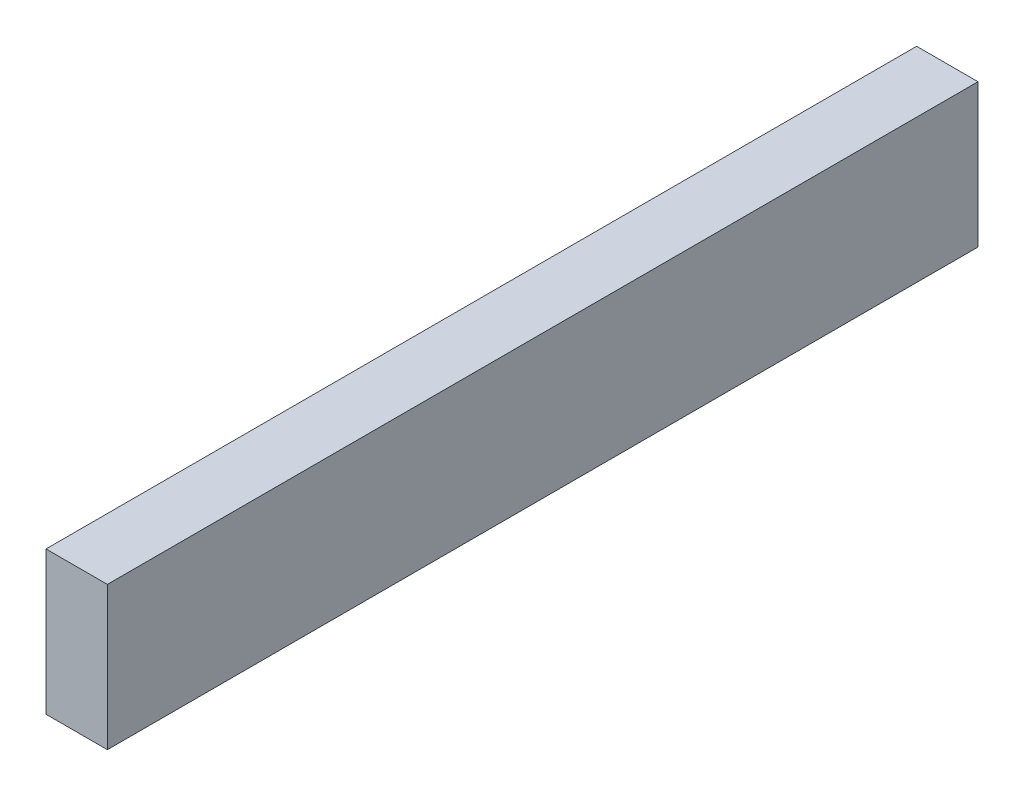
SolidWorks part; units mm, degrees
material "Pine"
ref_plane "Front Plane" through (0, 0, 0) normal (0, 0, 1) x (1, 0, 0)
ref_plane "Top Plane" through (0, 0, 0) normal (0, 1, 0) x (1, 0, 0)
ref_plane "Right Plane" through (0, 0, 0) normal (1, 0, 0) x (0, 0, -1)
sketch "Sketch1" plane through (0, 0, 0) normal (0, 0, 1) x (1, 0, 0)
  line L1 (-2.38, 27.7705) -> (35.72, 27.7705)
  line L2 (-2.38, 27.7705) -> (-2.38, -61.1295)
  line L3 (-2.38, -61.1295) -> (35.72, -61.1295)
  line L4 (35.72, 27.7705) -> (35.72, -61.1295)
  dimension "D1" = 38.1
  dimension "D2" = 88.9
extrude "Boss-Extrude1" add sketch "Sketch1" along normal blind 540.5438
